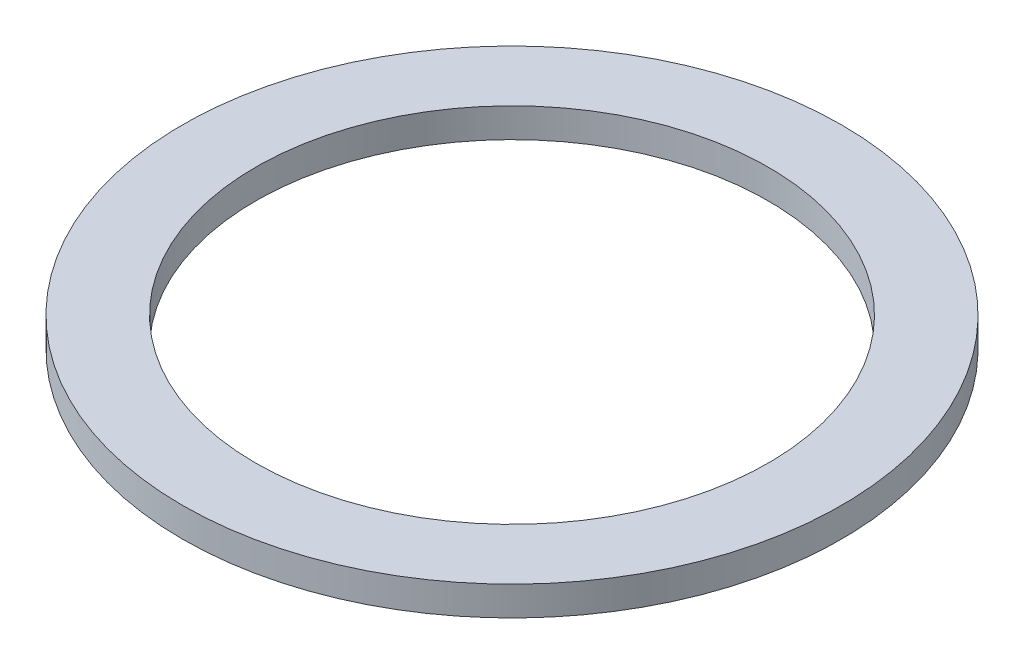
SolidWorks part; units mm, degrees
material "Acrílico (Impacto medio-alto)"
ref_plane "Alzado" through (0, 0, 0) normal (0, 0, 1) x (1, 0, 0)
ref_plane "Planta" through (0, 0, 0) normal (0, 1, 0) x (1, 0, 0)
ref_plane "Vista lateral" through (0, 0, 0) normal (1, 0, 0) x (0, 0, -1)
sketch "Croquis1" plane through (0, 0, 0) normal (0, 1, 0) x (1, 0, 0)
  circle A0 centre (0, 0) radius 45
  circle A1 centre (0, 0) radius 35
  dimension "D1" = 90
  dimension "D2" = 10
extrude "Saliente-Extruir1" add sketch "Croquis1" along normal blind 4 contours A1
equation "\"4\"= 4"
